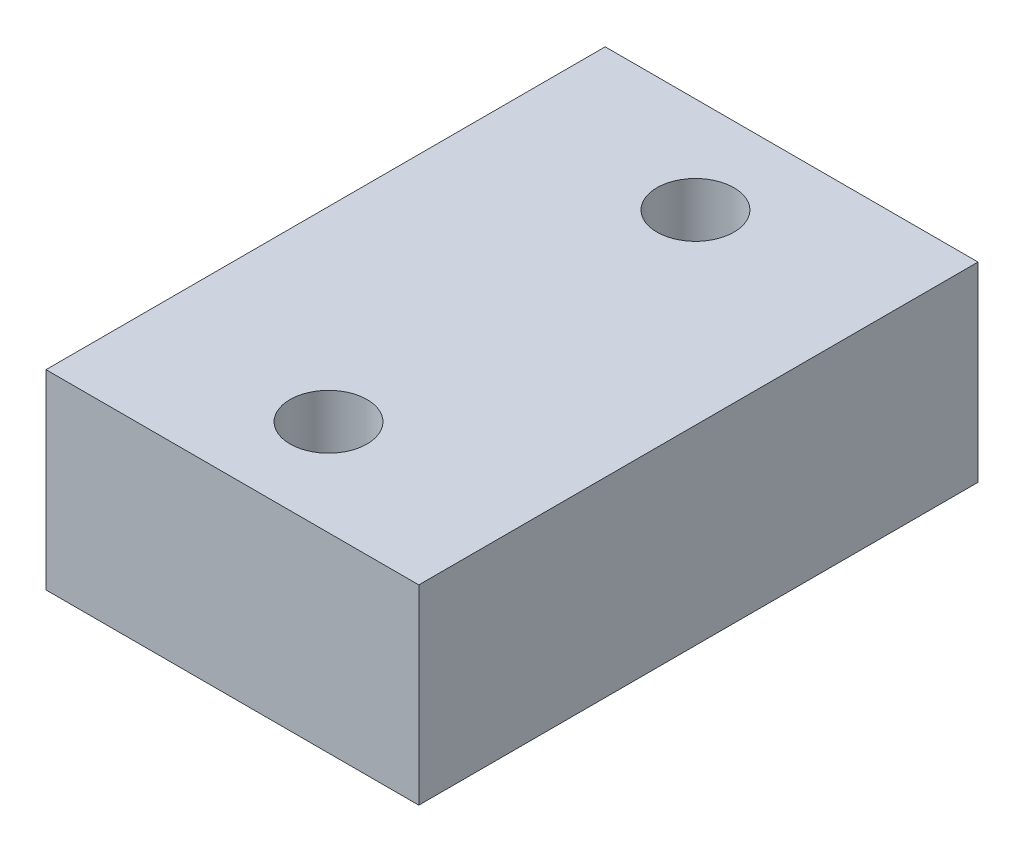
SolidWorks part; units mm, degrees
ref_plane "Front Plane" through (0, 0, 0) normal (0, 0, 1) x (1, 0, 0)
ref_plane "Top Plane" through (0, 0, 0) normal (0, 1, 0) x (1, 0, 0)
ref_plane "Right Plane" through (0, 0, 0) normal (1, 0, 0) x (0, 0, -1)
sketch "Sketch1" plane through (0, 0, 0) normal (0, 1, 0) x (1, 0, 0)
  line L1 (-25.4, -38.1) -> (25.4, -38.1)
  line L2 (-25.4, -38.1) -> (-25.4, 38.1)
  line L3 (-25.4, 38.1) -> (25.4, 38.1)
  line L4 (25.4, -38.1) -> (25.4, 38.1)
  line L5 (-25.4, -38.1) -> (25.4, 38.1) construction
  line L6 (-25.4, 38.1) -> (25.4, -38.1) construction
  point P0 (0, 0)
  dimension "D1" = 50.8
  dimension "D2" = 76.2
extrude "Boss-Extrude1" add sketch "Sketch1" along normal blind 26
sketch "Sketch2" plane through (0, 26, 0) normal (0, 1, 0) x (1, 0, 0)
  line L0 (0, 0) -> (0, 25)
  line L1 (0, 0) -> (0, -25)
  circle A0 centre (0, 25) radius 5.25
  circle A1 centre (0, -25) radius 5.25
  dimension "D1" = 25
  dimension "D2" = 25
extrude "Cut-Extrude2" cut sketch "Sketch2" against normal through all contours A0 | A1
